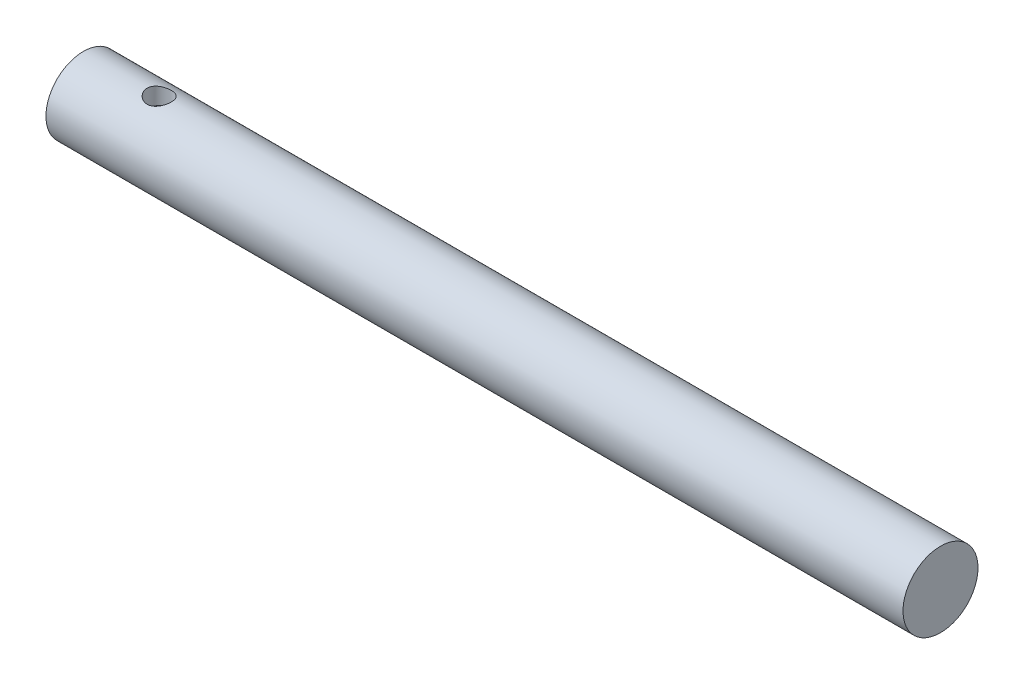
SolidWorks part; units mm, degrees
ref_plane "Front Plane" through (0, 0, 0) normal (0, 0, 1) x (1, 0, 0)
ref_plane "Top Plane" through (0, 0, 0) normal (0, 1, 0) x (1, 0, 0)
ref_plane "Right Plane" through (0, 0, 0) normal (1, 0, 0) x (0, 0, -1)
sketch "Sketch1" plane through (0, 0, 0) normal (1, 0, 0) x (0, 0, -1)
  circle A0 centre (0, 0) radius 3.1115
  dimension "D1" = 6.223
extrude "Boss-Extrude1" add sketch "Sketch1" along normal blind 71.12
sketch "Sketch2" plane through (0, 0, 0) normal (-1, 0, 0) x (0, 0, 1)
  line L0 (-1.1516, 1.651) -> (1.1516, 1.651)
  arc A0 (-1.1516, 1.651) -> (1.1516, 1.651) centre (0, 0) ccw
  dimension "D1" = 4.0259
  dimension "D2" = 1.651
extrude "Cut-Extrude1" cut sketch "Sketch2" against normal blind 12
sketch "Sketch3" plane through (0, 1.651, 0) normal (0, -1, 0) x (1, 0, 0)
  circle A0 centre (6.2886, 0) radius 1
  dimension "D1" = 2
extrude "Cut-Extrude2" cut sketch "Sketch3" against normal blind 2.54
